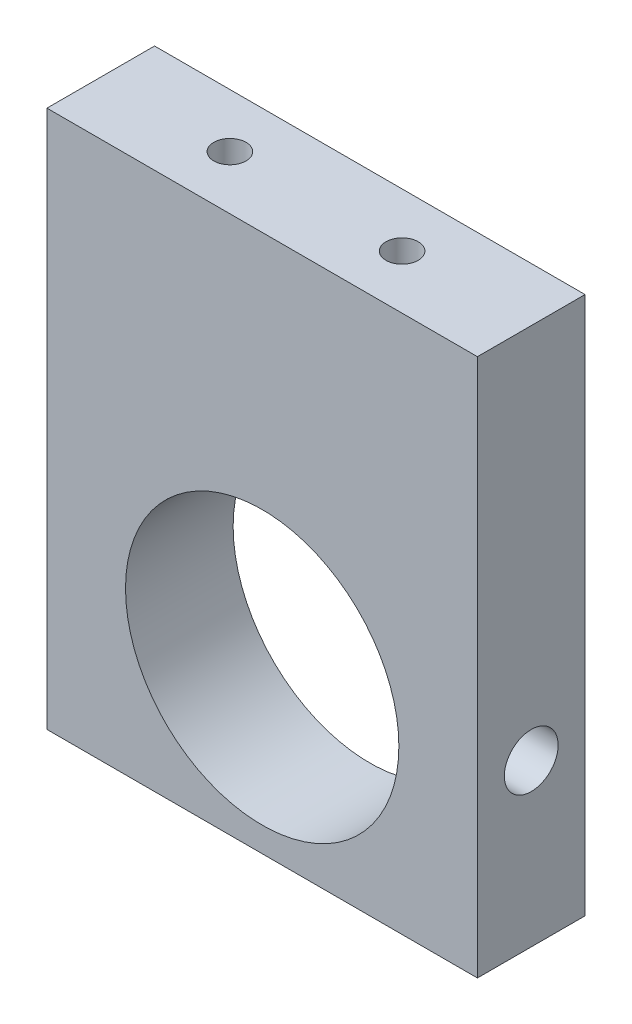
SolidWorks part; units mm, degrees
ref_plane "Front Plane" through (0, 0, 0) normal (0, 0, 1) x (1, 0, 0)
ref_plane "Top Plane" through (0, 0, 0) normal (0, 1, 0) x (1, 0, 0)
ref_plane "Right Plane" through (0, 0, 0) normal (1, 0, 0) x (0, 0, -1)
sketch "Sketch1" plane through (0, 0, 0) normal (0, 0, 1) x (1, 0, 0)
  line L1 (-24.0859, 31.833) -> (-4.0859, 31.833)
  line L2 (-24.0859, 31.833) -> (-24.0859, 6.833)
  line L3 (-24.0859, 6.833) -> (-4.0859, 6.833)
  line L4 (-4.0859, 31.833) -> (-4.0859, 6.833)
  dimension "D1" = 20
  dimension "D2" = 25
extrude "Boss-Extrude1" add sketch "Sketch1" along normal blind 5
sketch "Sketch3" plane through (0, 0, 5) normal (0, 0, 1) x (1, 0, 0)
  line L0 (-4.0859, 31.833) -> (-24.0859, 31.833) construction
  line L1 (-24.0859, 31.833) -> (-24.0859, 6.833) construction
  circle A0 centre (-14.0859, 14.333) radius 6.35
  dimension "D1" = 12.7
  dimension "D2" = 17.5
  dimension "D3" = 10
extrude "Cut-Extrude1" cut sketch "Sketch3" against normal up to next
sketch "Sketch5" plane through (0, 31.833, 0) normal (0, 1, 0) x (1, 0, 0)
  line L0 (-4.0859, -5) -> (-4.0859, 0) construction
  line L1 (-24.0859, -5) -> (-24.0859, 0) construction
  line L2 (-4.0859, 0) -> (-24.0859, 0) construction
  circle A0 centre (-10.0859, -2.5) radius 0.75
  circle A1 centre (-18.0859, -2.5) radius 0.75
  point P6 (-24.0859, -2.5)
  dimension "D3" = 1.5
  dimension "D4" = 1.5
  dimension "D1" = 6
  dimension "D2" = 6
  dimension "D5" = 2.5
  dimension "D6" = 2.5
extrude "Cut-Extrude2" cut sketch "Sketch5" against normal blind 7
sketch "Sketch6" plane through (-4.0859, 0, 0) normal (1, 0, 0) x (0, 0, -1)
  line L0 (-5, 31.833) -> (0, 31.833) construction
  line L1 (0, 6.833) -> (0, 31.833) construction
  circle A0 centre (-2.5, 14.333) radius 1.25
  dimension "D1" = 17.5
  dimension "D2" = 2.5
  dimension "D3" = 2.5
extrude "Cut-Extrude3" cut sketch "Sketch6" against normal up to next
